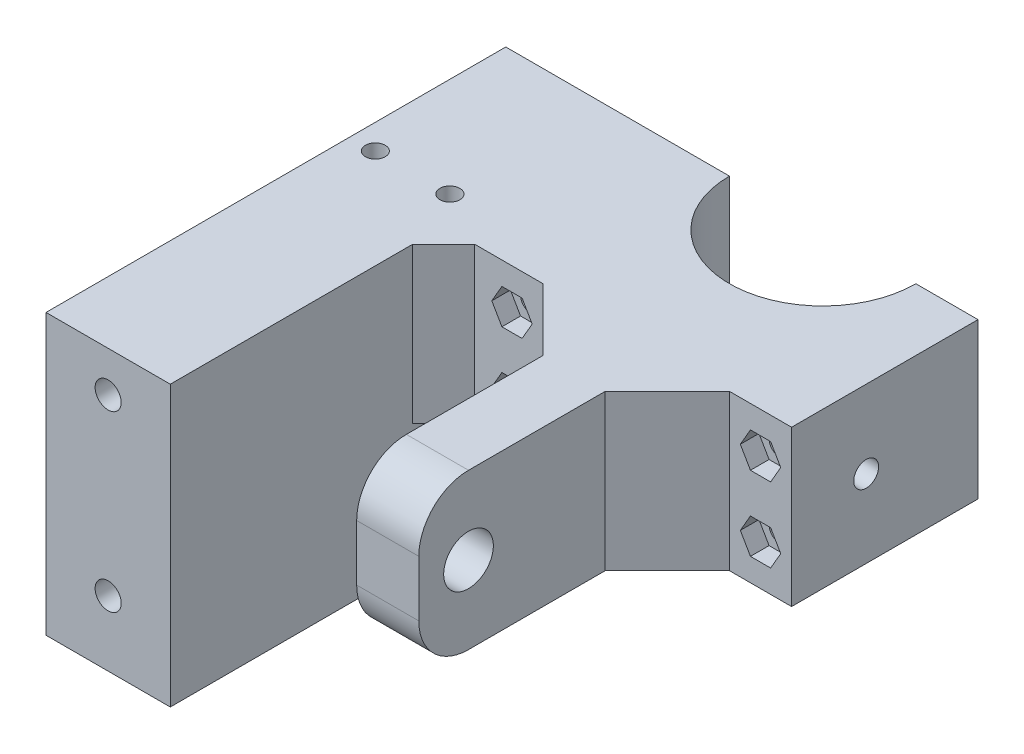
SolidWorks part; units mm, degrees
ref_plane "Спереди" through (0, 0, 0) normal (0, 0, 1) x (1, 0, 0)
ref_plane "Сверху" through (0, 0, 0) normal (0, 1, 0) x (1, 0, 0)
ref_plane "Справа" through (0, 0, 0) normal (1, 0, 0) x (0, 0, -1)
sketch "Sketch1" plane through (0, 0, 0) normal (0, 1, 0) x (1, 0, 0)
  line L0 (26.0276, -8) -> (-23.9724, -8) construction
  line L1 (-13.9724, -8) -> (-23.9724, -8)
  line L2 (-23.9724, -8) -> (-23.9724, -38)
  line L3 (-23.9724, -38) -> (-3.9724, -38)
  line L4 (-3.9724, -38) -> (-3.9724, -78)
  line L5 (-3.9724, -78) -> (6.0276, -78)
  line L6 (6.0276, -78) -> (6.0276, -38)
  line L7 (6.0276, -38) -> (26.0276, -38)
  line L8 (26.0276, -38) -> (26.0276, -8)
  line L9 (16.0276, -8) -> (26.0276, -8)
  circle A0 centre (1.0276, -8) radius 15 construction
  arc A1 (-13.9724, -8) -> (16.0276, -8) centre (1.0276, -8) ccw
  dimension "D2" = 30
  dimension "D1" = 30
  dimension "D3" = 10
  dimension "D4" = 40
  dimension "D5" = 50
extrude "Boss-Extrude1" add sketch "Sketch1" along normal blind 25
sketch "Sketch2" plane through (-3.9724, 0, 0) normal (-1, 0, 0) x (0, 0, 1)
  line L0 (78, 12.5) -> (38, 12.5) construction
  line L1 (78, 25) -> (78, 0) construction
  line L2 (38, 25) -> (38, 0) construction
  circle A0 centre (70, 12.5) radius 4
  dimension "D1" = 8
  dimension "D2" = 8
extrude "Cut-Extrude1" cut sketch "Sketch2" against normal through all
sketch "Sketch3" plane through (0, 0, 8) normal (0, 0, -1) x (-1, 0, 0)
  line L0 (-21.0276, 0) -> (-21.0276, 25) construction
  line L1 (-26.0276, 0) -> (-16.0276, 0) construction
  line L2 (-26.0276, 25) -> (-16.0276, 25) construction
  line L3 (18.9724, 0) -> (18.9724, 25) construction
  line L4 (13.9724, 0) -> (23.9724, 0) construction
  line L5 (13.9724, 25) -> (23.9724, 25) construction
  line L6 (-21.0276, 6.5) -> (18.9724, 6.5) construction
  line L7 (-21.0276, 18.5) -> (18.9724, 18.5) construction
  circle A0 centre (-21.0276, 6.5) radius 1.6
  circle A1 centre (-21.0276, 18.5) radius 1.6
  circle A2 centre (18.9724, 6.5) radius 1.6
  circle A3 centre (18.9724, 18.5) radius 1.6
  point P16 (-21.0276, 12.5)
  dimension "D2" = 3.2
  dimension "D3" = 12
  dimension "D4" = 6
extrude "Cut-Extrude2" cut sketch "Sketch3" against normal through all
sketch "Sketch4" plane through (0, 0, 38) normal (0, 0, 1) x (1, 0, 0)
  line L1 (24.2776, 18.5) -> (22.6526, 21.3146)
  line L2 (22.6526, 21.3146) -> (19.4026, 21.3146)
  line L3 (19.4026, 21.3146) -> (17.7776, 18.5)
  line L4 (17.7776, 18.5) -> (19.4026, 15.6854)
  line L5 (19.4026, 15.6854) -> (22.6526, 15.6854)
  line L6 (22.6526, 15.6854) -> (24.2776, 18.5)
  line L7 (24.2776, 6.5) -> (22.6526, 9.3146)
  line L8 (22.6526, 9.3146) -> (19.4026, 9.3146)
  line L9 (19.4026, 9.3146) -> (17.7776, 6.5)
  line L10 (17.7776, 6.5) -> (19.4026, 3.6854)
  line L11 (19.4026, 3.6854) -> (22.6526, 3.6854)
  line L12 (22.6526, 3.6854) -> (24.2776, 6.5)
  line L13 (-15.7224, 18.5) -> (-17.3474, 21.3146)
  line L14 (-17.3474, 21.3146) -> (-20.5974, 21.3146)
  line L15 (-20.5974, 21.3146) -> (-22.2224, 18.5)
  line L16 (-22.2224, 18.5) -> (-20.5974, 15.6854)
  line L17 (-20.5974, 15.6854) -> (-17.3474, 15.6854)
  line L18 (-17.3474, 15.6854) -> (-15.7224, 18.5)
  line L19 (-15.7224, 6.5) -> (-17.3474, 9.3146)
  line L20 (-17.3474, 9.3146) -> (-20.5974, 9.3146)
  line L21 (-20.5974, 9.3146) -> (-22.2224, 6.5)
  line L22 (-22.2224, 6.5) -> (-20.5974, 3.6854)
  line L23 (-20.5974, 3.6854) -> (-17.3474, 3.6854)
  line L24 (-17.3474, 3.6854) -> (-15.7224, 6.5)
  circle A0 centre (21.0276, 18.5) radius 3.25 construction
  circle A1 centre (21.0276, 6.5) radius 3.25 construction
  circle A2 centre (-18.9724, 18.5) radius 3.25 construction
  circle A3 centre (-18.9724, 6.5) radius 3.25 construction
  dimension "D1" = 6.5
extrude "Cut-Extrude3" cut sketch "Sketch4" against normal blind 3
fillet "Fillet2" radius 8 2 edges at (1.0276, 0, 78) (1.0276, 25, 78)
chamfer "Chamfer2" distance 10 angle 45 2 edges at (6.0276, 12.5, 38) (-3.9724, 12.5, 38)
sketch "Sketch5" plane through (-23.9724, 0, 0) normal (-1, 0, 0) x (0, 0, 1)
  line L0 (8, 12.5) -> (38, 12.5) construction
  line L1 (8, 25) -> (8, 0) construction
  line L2 (38, 25) -> (38, 0) construction
  line L4 (38, 25) -> (8, 25)
  line L5 (38, 25) -> (38, 0)
  line L6 (38, 0) -> (8, 0)
  line L7 (8, 25) -> (8, 0)
  line L8 (38, 25) -> (8, 0) construction
  line L9 (38, 0) -> (8, 25) construction
  point P6 (23, 12.5)
extrude "Boss-Extrude2" add sketch "Sketch5" along normal blind 26
sketch "Sketch6" plane through (0, 0, 38) normal (0, 0, 1) x (1, 0, 0)
  line L0 (-39.9701, 0) -> (-39.9701, 25) construction
  line L1 (-49.9724, 0) -> (-13.9724, 0) construction
  line L2 (-49.9724, 25) -> (-13.9724, 25) construction
  line L4 (-29.9679, 25) -> (-49.9724, 25)
  line L5 (-29.9679, 25) -> (-29.9679, 0)
  line L6 (-29.9679, 0) -> (-49.9724, 0)
  line L7 (-49.9724, 25) -> (-49.9724, 0)
  line L8 (-29.9679, 25) -> (-49.9724, 0) construction
  line L9 (-29.9679, 0) -> (-49.9724, 25) construction
  point P6 (-39.9701, 12.5)
  dimension "D1" = 20.0045
extrude "Boss-Extrude3" add sketch "Sketch6" along normal blind 44
sketch "Sketch7" plane through (0, 0, 0) normal (0, -1, 0) x (1, 0, 0)
  line L0 (-29.9679, 66) -> (-49.9724, 66) construction
  line L1 (-29.9679, 82) -> (-29.9679, 38) construction
  line L2 (-49.9724, 8) -> (-49.9724, 82) construction
  line L3 (-49.9724, 82) -> (-29.9679, 82) construction
  line L4 (-45.1701, 76.2) -> (-34.7701, 76.2)
  line L5 (-45.1701, 76.2) -> (-45.1701, 55.8)
  line L6 (-45.1701, 55.8) -> (-34.7701, 55.8)
  line L7 (-34.7701, 76.2) -> (-34.7701, 55.8)
  line L8 (-45.1701, 76.2) -> (-34.7701, 55.8) construction
  line L9 (-45.1701, 55.8) -> (-34.7701, 76.2) construction
  point P6 (-39.9701, 66)
  dimension "D1" = 10.4
  dimension "D2" = 20.4
  dimension "D3" = 16
extrude "Cut-Extrude4" cut sketch "Sketch7" against normal blind 23
sketch "Sketch9" plane through (0, 0, 0) normal (0, -1, 0) x (1, 0, 0)
  line L0 (-45.1701, 66) -> (-34.7701, 66) construction
  line L1 (-45.1701, 76.2) -> (-45.1701, 55.8) construction
  line L2 (-34.7701, 55.8) -> (-34.7701, 76.2) construction
  line L3 (-49.9724, 82) -> (-29.9679, 82) construction
  line L4 (-49.9724, 82) -> (-29.9679, 82)
  line L5 (-49.9724, 82) -> (-49.9724, 38)
  line L6 (-49.9724, 38) -> (-29.9679, 38)
  line L7 (-29.9679, 82) -> (-29.9679, 38)
  line L8 (-34.7701, 76.2) -> (-45.1701, 76.2) construction
  line L10 (-45.1701, 76.2) -> (-34.7701, 76.2)
  line L11 (-45.1701, 76.2) -> (-45.1701, 55.8)
  line L12 (-45.1701, 55.8) -> (-34.7701, 55.8)
  line L13 (-34.7701, 76.2) -> (-34.7701, 55.8)
  line L14 (-45.1701, 76.2) -> (-34.7701, 55.8) construction
  line L15 (-45.1701, 55.8) -> (-34.7701, 76.2) construction
  point P6 (-39.9701, 66)
  point P12 (-39.9701, 66)
extrude "Boss-Extrude4" add sketch "Sketch9" along normal blind 20
sketch "Sketch10" plane through (0, 0, 82) normal (0, 0, 1) x (1, 0, 0)
  line L0 (-39.9701, -20) -> (-39.9701, 25) construction
  line L1 (-29.9679, -20) -> (-49.9724, -20) construction
  line L2 (-29.9679, 25) -> (-49.9724, 25) construction
  circle A0 centre (-39.9701, -9.5) radius 2.1
  circle A1 centre (-39.9701, 18.5) radius 2.1
  point P16 (-39.9701, 2.5)
  dimension "D1" = 28
  dimension "D2" = 4.2
  dimension "D3" = 12
extrude "Cut-Extrude6" cut sketch "Sketch10" against normal through all
chamfer "Chamfer5" distance 5 angle 45 1 edges at (-29.9679, 12.5, 38)
sketch "Sketch11" plane through (26.0276, 0, 0) normal (1, 0, 0) x (0, 0, -1)
  line L0 (-8, 12.5) -> (-38, 12.5) construction
  line L1 (-8, 25) -> (-8, 0) construction
  line L2 (-38, 25) -> (-38, 0) construction
  circle A0 centre (-26, 12.5) radius 2
  dimension "D1" = 4
  dimension "D2" = 18
extrude "Cut-Extrude7" cut sketch "Sketch11" against normal through all
sketch "Sketch12" plane through (0, 0, 38) normal (0, 0, -1) x (-1, 0, 0)
  line L0 (29.9679, -10) -> (49.9724, -10) construction
  line L1 (29.9679, -20) -> (29.9679, 0) construction
  line L2 (49.9724, -20) -> (49.9724, 0) construction
  line L4 (49.9724, -20) -> (29.9679, -20)
  line L5 (49.9724, -20) -> (49.9724, 0)
  line L6 (49.9724, 0) -> (29.9679, 0)
  line L7 (29.9679, -20) -> (29.9679, 0)
  line L8 (49.9724, -20) -> (29.9679, 0) construction
  line L9 (49.9724, 0) -> (29.9679, -20) construction
  circle A0 centre (39.9701, -9.5) radius 2.1
  point P6 (39.9701, -10)
extrude "Boss-Extrude5" add sketch "Sketch12" along normal up to surface (30 mm away) up to face at (-37.8701, 18.5, 8)
sketch "Sketch13" plane through (0, -20, 0) normal (0, -1, 0) x (1, 0, 0)
  line L0 (-29.9679, 33) -> (-49.9724, 33) construction
  line L1 (-29.9679, 8) -> (-29.9679, 82) construction
  line L2 (-49.9724, 82) -> (-49.9724, 8) construction
  line L3 (-49.9724, 8) -> (-29.9679, 8) construction
  circle A0 centre (-33.9701, 33) radius 1.6
  circle A1 centre (-45.9701, 33) radius 1.6
  point P10 (-39.9701, 33)
  dimension "D1" = 3.2
  dimension "D2" = 12
  dimension "D3" = 6
  dimension "D4" = 25
extrude "Cut-Extrude8" cut sketch "Sketch13" against normal through all
